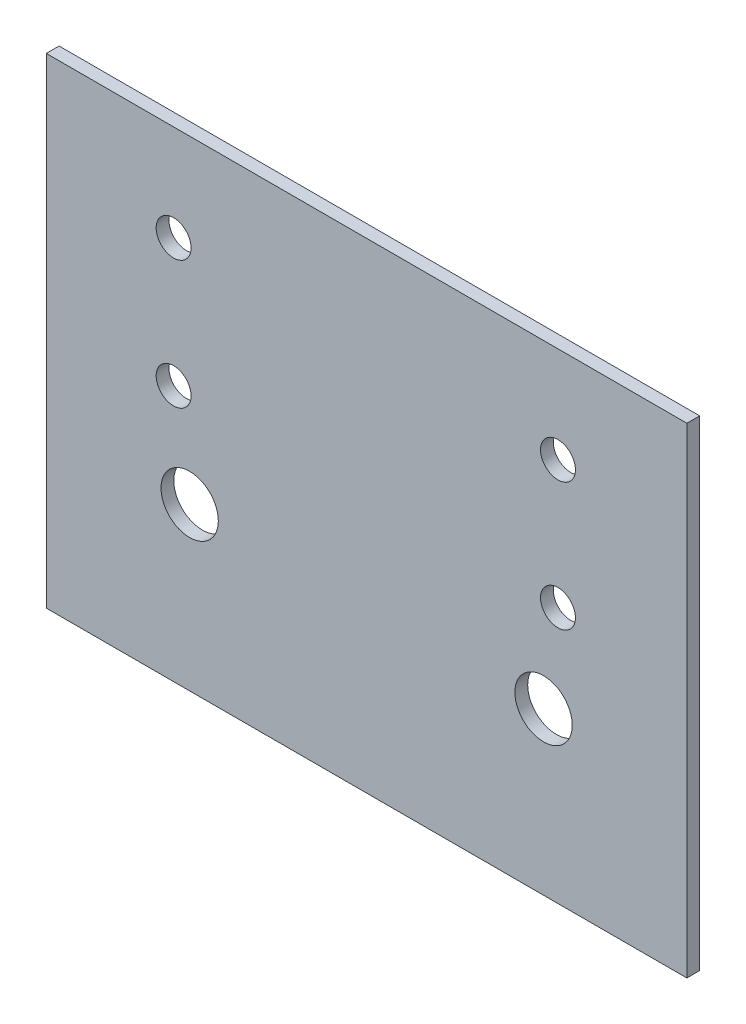
SolidWorks part; units mm, degrees
ref_plane "前视基准面" through (0, 0, 0) normal (0, 0, 1) x (1, 0, 0)
ref_plane "上视基准面" through (0, 0, 0) normal (0, 1, 0) x (1, 0, 0)
ref_plane "右视基准面" through (0, 0, 0) normal (1, 0, 0) x (0, 0, -1)
sketch "草图1" plane through (0, 0, 0) normal (0, 0, 1) x (1, 0, 0)
  line L0 (-55.1061, 34.2026) -> (344.8939, 34.2026)
  line L1 (-55.1061, 34.2026) -> (-55.1061, -265.7974)
  line L2 (-55.1061, -265.7974) -> (344.8939, -265.7974)
  line L3 (344.8939, -265.7974) -> (344.8939, 34.2026)
  circle A0 centre (24.3979, -25.7974) radius 10.9
  circle A1 centre (264.3979, -25.7974) radius 10.9
  circle A8 centre (24.3979, -105.7974) radius 10.9
  circle A9 centre (264.3979, -105.7974) radius 10.9
  circle A12 centre (34.3979, -164.9582) radius 17.9
  circle A13 centre (255.3899, -164.9582) radius 17.9
extrude "凸台-拉伸1" add sketch "草图1" along normal blind 8
